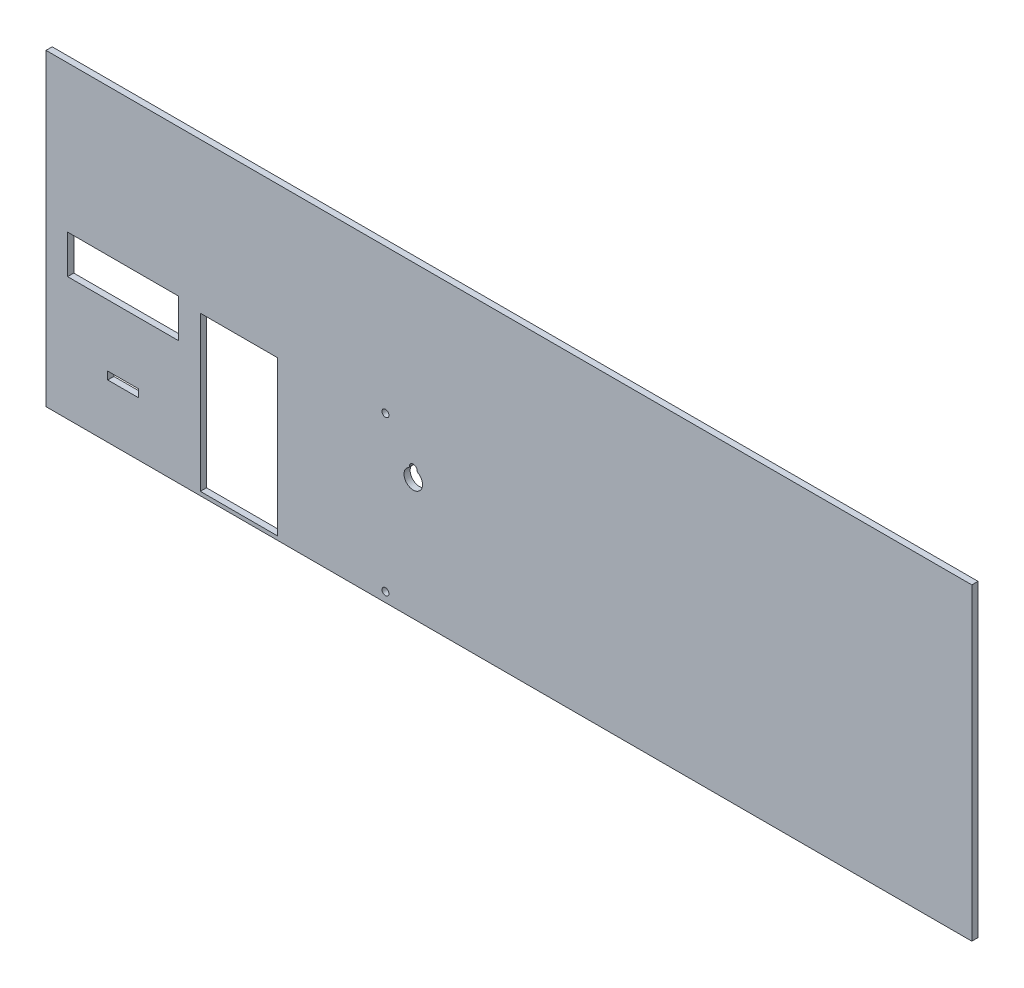
SolidWorks part; units mm, degrees
material "Balsa"
ref_plane "Front Plane" through (0, 0, 0) normal (0, 0, 1) x (1, 0, 0)
ref_plane "Top Plane" through (0, 0, 0) normal (0, 1, 0) x (1, 0, 0)
ref_plane "Right Plane" through (0, 0, 0) normal (1, 0, 0) x (0, 0, -1)
sketch "Sketch1" plane through (0, 0, 0) normal (0, 0, 1) x (1, 0, 0)
  line L5 (600, 200) -> (0, 200)
  line L6 (600, 200) -> (600, 0)
  line L7 (600, 0) -> (0, 0)
  line L8 (0, 200) -> (0, 0)
  line L13 (150, 102.5) -> (100, 102.5)
  line L14 (150, 102.5) -> (150, 2.5)
  line L15 (150, 2.5) -> (100, 2.5)
  line L16 (100, 102.5) -> (100, 2.5)
  line L17 (248.9946, 108.5597) -> (158.9946, 108.5597) construction
  line L18 (158.9946, 8.4403) -> (248.9946, 8.4403) construction
  line L19 (40, 40) -> (60, 40)
  line L20 (40, 40) -> (40, 35)
  line L21 (40, 35) -> (60, 35)
  line L22 (60, 40) -> (60, 35)
  line L23 (14, 105) -> (86, 105)
  line L24 (14, 105) -> (14, 80)
  line L25 (14, 80) -> (86, 80)
  line L26 (86, 105) -> (86, 80)
  circle A0 centre (220, 106.3097) radius 2.25
  circle A2 centre (220, 6.1903) radius 2.25
  arc A3 (234.9573, 83.3712) -> (241.0427, 83.3712) centre (238, 78.2) ccw
  arc A7 (240.5499, 84.2238) -> (235.4501, 84.2238) centre (238, 84.2) ccw
  arc A8 (234.9573, 83.3712) -> (235.4501, 84.2238) centre (234.4502, 84.2331) ccw
  arc A9 (240.5499, 84.2238) -> (241.0427, 83.3712) centre (241.5498, 84.2331) ccw
  point P29 (50, 40)
  dimension "D7" = 4.5
  dimension "D8" = 4.5
  dimension "D10" = 12
  dimension "D11" = 78.2
  dimension "D12" = 238
  dimension "D13" = 5.1
  dimension "D14" = 1
  dimension "D1" = 600
  dimension "D2" = 200
  dimension "D3" = 100
  dimension "D4" = 50
  dimension "D5" = 2.5
  dimension "D6" = 100
  dimension "D9" = 70
  dimension "D15" = 20
  dimension "D16" = 5
  dimension "D17" = 50
  dimension "D18" = 35
  dimension "D19" = 25
  dimension "D20" = 72
  dimension "D21" = 80
  dimension "D22" = 14
extrude "Boss-Extrude1" add sketch "Sketch1" along normal blind 4
